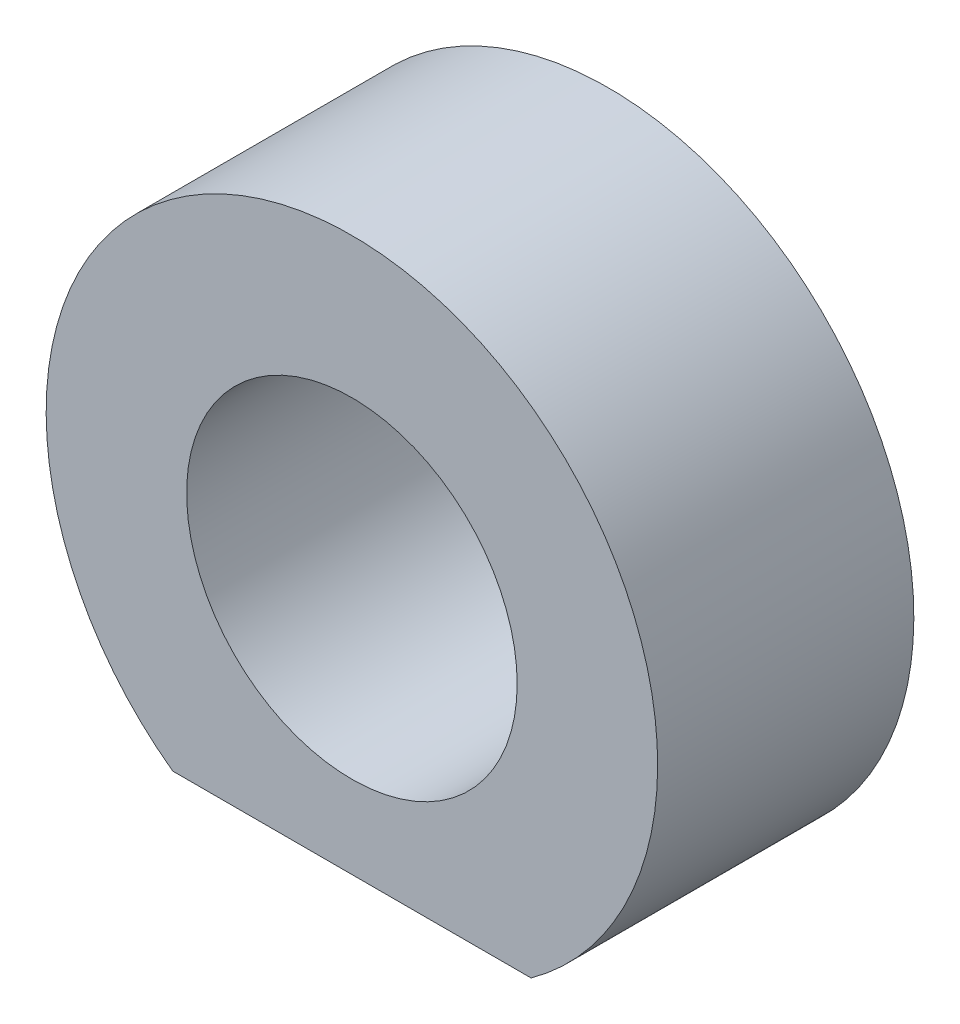
SolidWorks part; units mm, degrees
ref_plane "Front Plane" through (0, 0, 0) normal (0, 0, 1) x (1, 0, 0)
ref_plane "Top Plane" through (0, 0, 0) normal (0, 1, 0) x (1, 0, 0)
ref_plane "Right Plane" through (0, 0, 0) normal (1, 0, 0) x (0, 0, -1)
sketch "Sketch1" plane through (0, 0, 0) normal (0, 0, 1) x (1, 0, 0)
  line L1 (-10.842, -14.99) -> (10.842, -14.99)
  arc A0 (10.842, -14.99) -> (-10.842, -14.99) centre (0, 0) ccw
  circle A1 centre (0, 0) radius 10
  point P8 (0, 0)
  point P9 (0, -14.99)
  dimension "D1" = 37
  dimension "D2" = 20
  dimension "D3" = 21.6841
extrude "Boss-Extrude1" add sketch "Sketch1" along normal blind 15.5
